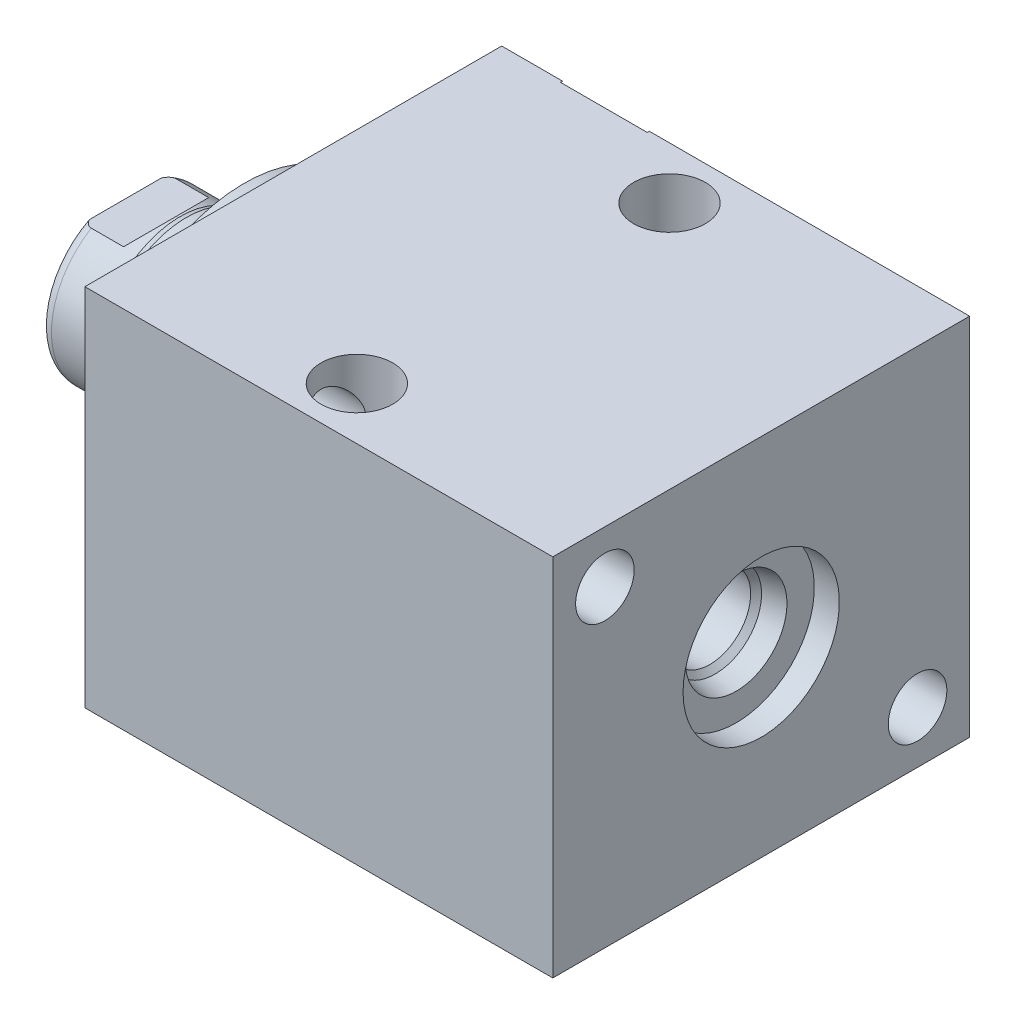
SolidWorks part; units mm, degrees
material "Alloy Steel"
ref_plane "Front Plane" through (0, 0, 0) normal (0, 0, 1) x (1, 0, 0)
ref_plane "Top Plane" through (0, 0, 0) normal (0, 1, 0) x (1, 0, 0)
ref_plane "Right Plane" through (0, 0, 0) normal (1, 0, 0) x (0, 0, -1)
ref_plane "Plane1" through (0, 0, 0) normal (1, 0, 0) x (0, 0, -1)
sketch "Sketch1" plane through (0, 0, 0) normal (1, 0, 0) x (0, 0, -1)
  line L0 (-25.4, 22.225) -> (25.4, 22.225)
  line L1 (25.4, 22.225) -> (25.4, -22.225)
  line L2 (25.4, -22.225) -> (-25.4, -22.225)
  line L3 (-25.4, -22.225) -> (-25.4, 22.225)
  line L4 (0, -24.4475) -> (0, 24.4475) construction
  dimension "D1" = 44.45
  dimension "D2" = 22.225
  dimension "D3" = 50.8
extrude "Extrude1" add sketch "Sketch1" along normal blind 57.023
ref_plane "Plane12" through (0, 14.3002, 0) normal (0, 1, 0) x (-1, 0, 0)
sketch "S2D0002" plane through (0, 14.3002, 0) normal (0, 1, 0) x (-1, 0, 0)
  line L0 (-18.8849, -25.146) -> (-22.225, -25.146)
  line L1 (-18.8849, -25.146) -> (-18.3423, -22.5933)
  line L2 (-18.3423, -22.5933) -> (-17.6784, -21.9294)
  line L3 (-17.6784, -21.9294) -> (-17.6784, -11.176)
  line L4 (-17.6784, -11.176) -> (-12.7, -11.176)
  line L5 (-12.7, -11.176) -> (-12.7, -25.4)
  line L6 (-12.7, -19.1384) -> (-12.7, 0.6985) construction
  line L7 (0, -25.4) -> (0, 25.4) construction
  line L8 (-22.225, -25.4) -> (-22.225, -25.146)
  line L9 (-57.023, -25.4) -> (0, -25.4) construction
  line L10 (-22.225, -25.4) -> (-12.7, -25.4)
  dimension "D1" = 14.224
  dimension "D2" = 12.7
  dimension "D3" = 9.9568
  dimension "D4" = 45
  dimension "D5" = 12.3698
  dimension "D6" = 12
  dimension "D7" = 2.5527
  dimension "D8" = 0.254
  dimension "D9" = 19.05
revolve "Cut-Revolve1" cut sketch "S2D0002" angle 360 about L6
ref_plane "Plane3" through (41.148, 0, -25.146) normal (0, 1, 0) x (1, 0, 0)
sketch "Sketch3" plane through (41.148, 0, -25.146) normal (0, 1, 0) x (1, 0, 0)
  line L0 (6.1849, 0) -> (9.525, 0)
  line L1 (6.1849, 0) -> (5.6423, -2.5527)
  line L2 (5.6423, -2.5527) -> (4.9784, -3.2166)
  line L3 (4.9784, -3.2166) -> (4.9784, -13.97)
  line L4 (4.9784, -13.97) -> (0, -13.97)
  line L5 (0, -13.97) -> (0, 0.254)
  line L6 (0, -21.9564) -> (0, 0.6985) construction
  line L7 (-41.148, 0.254) -> (-41.148, -50.546) construction
  line L8 (9.525, 0.254) -> (9.525, 0)
  line L9 (15.875, 0.254) -> (-23.1638, 0.254) construction
  line L10 (9.525, 0.254) -> (0, 0.254)
  dimension "D1" = 14.224
  dimension "D2" = 41.148
  dimension "D3" = 9.9568
  dimension "D4" = 45
  dimension "D5" = 12
  dimension "D6" = 12.3698
  dimension "D7" = 2.5527
  dimension "D8" = 0.254
  dimension "D9" = 19.05
revolve "Cut-Revolve2" cut sketch "Sketch3" angle 360 about L6
ref_plane "Plane4" through (53.975, 0, 0) normal (0, 0, 1) x (0, -1, 0)
sketch "Sketch4" plane through (53.975, 0, 0) normal (0, 0, 1) x (0, -1, 0)
  line L0 (6.1849, 0) -> (9.525, 0)
  line L1 (6.1849, 0) -> (5.6423, -2.5527)
  line L2 (5.6423, -2.5527) -> (4.9784, -3.2166)
  line L3 (4.9784, -3.2166) -> (4.9784, -11.3538)
  line L4 (4.9784, -11.3538) -> (0, -11.3538)
  line L5 (0, -11.3538) -> (0, 3.048)
  line L6 (0, -15.0954) -> (0, 0.5677) construction
  line L7 (0, 3.048) -> (9.525, 3.048)
  line L9 (-22.225, 3.048) -> (22.225, 3.048) construction
  line L10 (9.525, 3.048) -> (9.525, 0)
  dimension "D1" = 11.3538
  dimension "D2" = 9.9568
  dimension "D3" = 3.048
  dimension "D4" = 19.05
  dimension "D5" = 2.5527
  dimension "D6" = 12
  dimension "D7" = 45
  dimension "D8" = 12.3698
revolve "Cut-Revolve3" cut sketch "Sketch4" angle 360 about L6
sketch "Sketch5" plane through (0, 0, 0) normal (-1, 0, 0) x (0, 0, 1)
  circle A0 centre (0, 0) radius 17.4625
  dimension "D1" = 34.925
extrude "Extrude2" add sketch "Sketch5" along normal blind 5.969
ref_plane "Plane5" through (0, 0, 0) normal (0, -1, 0) x (0, 0, 1)
sketch "Sketch6" plane through (0, 0, 0) normal (0, -1, 0) x (0, 0, 1)
  line L0 (0, 5.969) -> (-10.3187, 5.969)
  line L1 (-10.3187, 5.969) -> (-10.3187, 20.447)
  line L2 (-10.3187, 20.447) -> (0, 20.447)
  line L3 (0, 20.447) -> (0, 5.969)
  line L4 (0, -5.7546) -> (0, 21.1709) construction
  line L5 (17.4625, 5.969) -> (-17.4625, 5.969) construction
  line L6 (25.4, -57.023) -> (-25.4, -57.023) construction
  dimension "D1" = 77.47
  dimension "D2" = 20.6375
revolve "Revolve1" add sketch "Sketch6" angle 360 about L4
ref_plane "Plane6" through (-18.5113, 3.2639, 0) normal (0, 0, 1) x (0, 1, 0)
sketch "S2D0001" plane through (-18.5113, 3.2639, 0) normal (0, 0, 1) x (0, 1, 0)
  line L0 (0, 0) -> (0, -14.6505)
  line L1 (0, -14.6505) -> (-3.2639, -14.6505)
  line L2 (1.1176, 1.9357) -> (-3.2639, 1.9357)
  line L3 (-3.2639, 1.9357) -> (-3.2639, -14.6505)
  line L4 (0, 0) -> (1.1176, 1.9357)
  line L5 (-3.2639, -18.5113) -> (-3.2639, 2.765) construction
  line L6 (7.0549, 1.9357) -> (-13.5826, 1.9357) construction
  dimension "D1" = 30
  dimension "D2" = 8.763
  dimension "D3" = 6.5278
  dimension "D4" = 16.5862
revolve "Cut-Revolve4" cut sketch "S2D0001" angle 360 about L5
ref_plane "Plane7" through (0, 0, 0) normal (0, 1, 0) x (0, 0, -1)
sketch "Sketch8" plane through (0, 0, 0) normal (0, 1, 0) x (0, 0, -1)
  line L0 (-10.3187, 13.0302) -> (-10.033, 13.7922)
  line L1 (-10.033, 13.7922) -> (-10.033, 19.431)
  line L2 (0, 12.6594) -> (0, 20.8178) construction
  line L3 (-10.3187, 13.0302) -> (-10.3187, 20.447)
  line L4 (-9.6449, 20.447) -> (-10.3187, 20.447)
  line L5 (10.3187, 20.447) -> (-10.3187, 20.447) construction
  line L6 (-10.3187, 20.447) -> (-10.3187, 5.969) construction
  arc A0 (-9.6449, 20.447) -> (-10.033, 19.431) centre (-8.509, 19.431) ccw
  dimension "D2" = 1.524
  dimension "D1" = 20.066
  dimension "D3" = 1.016
  dimension "D4" = 0.762
  dimension "D5" = 6.6548
revolve "Cut-Revolve5" cut sketch "Sketch8" angle 360 about L2
ref_plane "Plane11" through (0, 0, 0) normal (0, 0, -1) x (0, -1, 0)
sketch "Sketch12" plane through (0, 0, 0) normal (0, 0, -1) x (0, -1, 0)
  line L0 (8.5852, 20.447) -> (8.5852, 15.494)
  line L1 (8.5852, 15.494) -> (10.033, 14.0462)
  line L2 (-8.5852, 20.447) -> (-8.5852, 15.494)
  line L3 (-8.5852, 15.494) -> (-10.033, 14.0462)
  line L4 (8.5852, 20.447) -> (10.033, 20.447)
  line L5 (0, 13.7262) -> (0, 20.767) construction
  line L6 (-10.033, 14.0462) -> (-10.033, 20.447)
  line L7 (9.6449, 20.447) -> (-9.6449, 20.447) construction
  line L8 (10.033, 13.7922) -> (10.033, 19.431) construction
  line L9 (10.033, 14.0462) -> (10.033, 20.447)
  line L10 (-8.5852, 20.447) -> (-10.033, 20.447)
  dimension "D1" = 17.1704
  dimension "D2" = 4.953
  dimension "D3" = 45
extrude "Cut-Extrude4" cut sketch "Sketch12" against normal mid plane 60.96
hole_wizard "Hole1" positions "Sketch15" profile "Sketch14" legacy end condition up to next
sketch "Sketch15" plane through (0, 0, 0) normal (-1, 0, 0) x (0, 0, 1)
  line L0 (0, 0) -> (-29.9914, 0) construction
  line L1 (0, 0) -> (0, 25.7648) construction
  point P0 (-19.05, -15.875)
  point P11 (19.05, 15.875)
  dimension "D1" = 15.875
  dimension "D2" = 19.05
  dimension "D3" = 31.75
  dimension "D4" = 38.1
sketch "Sketch14" plane through (0, -15.875, -19.05) normal (0, 1, 0) x (0, 0, 1)
  line L0 (0, 0) -> (0, 57.023)
  line L1 (0, 57.023) -> (3.5687, 57.023)
  line L2 (3.5687, 57.023) -> (3.5687, 0)
  line L3 (3.5687, 0) -> (0, 0)
  line L4 (0, 110) -> (0, -10) construction
  dimension "Diameter" = 7.1374
  dimension "Depth" = 57.023
hole_wizard "Hole2" positions "Sketch17" profile "Sketch16" legacy
sketch "Sketch17" plane through (0, 22.225, 0) normal (0, 1, 0) x (-1, 0, 0)
  line L0 (0, 0) -> (-59.3363, 0) construction
  line L1 (0, -25.4) -> (0, 25.4) construction
  point P0 (-26.797, -19.05)
  point P9 (-26.797, 19.05)
  dimension "D1" = 38.1
  dimension "D2" = 26.797
sketch "Sketch16" plane through (26.797, 22.225, -19.05) normal (1, 0, 0) x (0, 0, 1)
  line L0 (0, 0) -> (0, 44.45)
  line L1 (0, 44.45) -> (4.3688, 44.45)
  line L2 (4.3688, 44.45) -> (4.3688, 0)
  line L3 (4.3688, 0) -> (0, 0)
  line L4 (0, 110) -> (0, -10) construction
  dimension "Diameter" = 8.7376
  dimension "Depth" = 44.45
